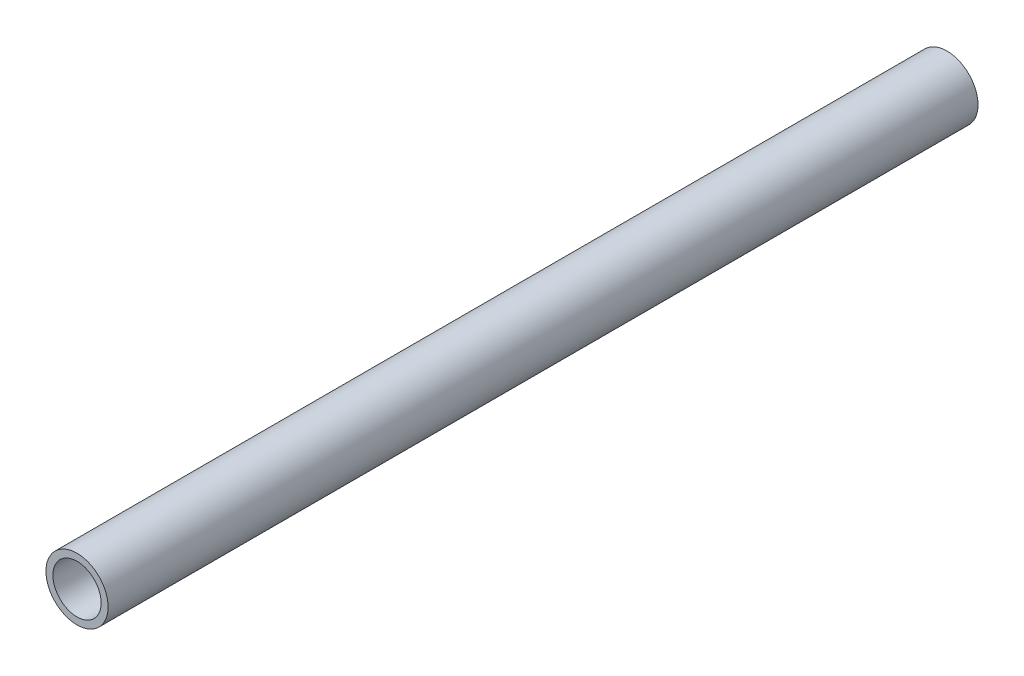
SolidWorks part; units mm, degrees
ref_plane "前视基准面" through (0, 0, 0) normal (0, 0, 1) x (1, 0, 0)
ref_plane "上视基准面" through (0, 0, 0) normal (0, 1, 0) x (1, 0, 0)
ref_plane "右视基准面" through (0, 0, 0) normal (1, 0, 0) x (0, 0, -1)
other "Configuration Table"
sketch "草图1" plane through (0, 0, 0) normal (0, 0, 1) x (1, 0, 0)
  circle A0 centre (0, 0) radius 12.5
  circle A1 centre (0, 0) radius 9.7
  dimension "D1" = 25
  dimension "D2" = 19.4
extrude "凸台-拉伸1" add sketch "草图1" along normal mid plane 350
